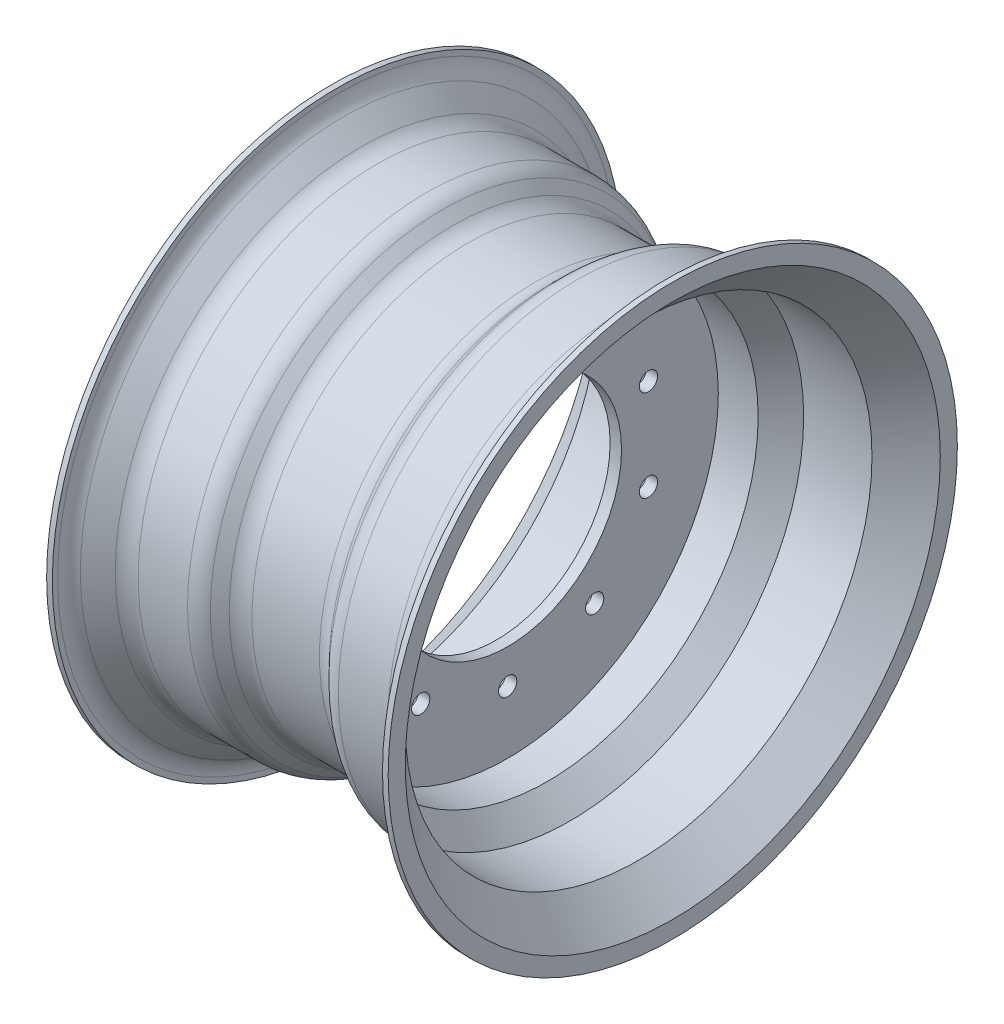
SolidWorks part; units mm, degrees
ref_plane "Front Plane" through (0, 0, 0) normal (0, 0, 1) x (1, 0, 0)
ref_plane "Top Plane" through (0, 0, 0) normal (0, 1, 0) x (1, 0, 0)
ref_plane "Right Plane" through (0, 0, 0) normal (1, 0, 0) x (0, 0, -1)
sketch "Sketch1" plane through (0, 0, 0) normal (0, 0, 1) x (1, 0, 0)
  line L0 (0, 221.1779) -> (0, 185) construction
  line L1 (0, 0) -> (-419.7995, 0) construction
  line L2 (-150, 250) -> (-150, 235)
  line L3 (-150, 235) -> (-120, 205)
  line L4 (-120, 205) -> (-60, 205)
  line L5 (-60, 205) -> (-40, 185)
  line L6 (-40, 185) -> (-5, 185)
  line L7 (60, 205) -> (40, 185)
  line L8 (120, 205) -> (60, 205)
  line L9 (150, 235) -> (120, 205)
  line L10 (150, 250) -> (150, 235)
  line L11 (-145, 250) -> (-145, 237.0711)
  line L12 (-145, 237.0711) -> (-117.9289, 210)
  line L13 (-117.9289, 210) -> (-57.9289, 210)
  line L14 (-57.9289, 210) -> (-37.9289, 190)
  line L15 (-37.9289, 190) -> (37.9289, 190)
  line L16 (57.9289, 210) -> (37.9289, 190)
  line L17 (117.9289, 210) -> (57.9289, 210)
  line L18 (145, 237.0711) -> (117.9289, 210)
  line L19 (145, 250) -> (145, 237.0711)
  line L20 (-150, 250) -> (-145, 250)
  line L21 (145, 250) -> (150, 250)
  line L22 (5, 185) -> (40, 185)
  line L24 (-5, 185) -> (-5, 100)
  line L25 (-5, 100) -> (5, 100)
  line L26 (5, 185) -> (5, 100)
  line L27 (-40, 185) -> (40, 185) construction
  line L28 (0, 100) -> (0, 0) construction
  point P10 (0, 185)
  dimension "D1" = 250
  dimension "D2" = 15
  dimension "D3" = 30
  dimension "D4" = 60
  dimension "D5" = 20
  dimension "D6" = 40
  dimension "D7" = 135
  dimension "D8" = 135
  dimension "D9" = 135
  dimension "D10" = 135
  dimension "D12" = 5
  dimension "D13" = 10
  dimension "D14" = 100
  dimension "D11" = 5
revolve "Revolve1" add sketch "Sketch1" angle 360 about L1
fillet "Fillet1" radius 20 8 edges at (117.9289, 0, -210) (57.9289, 0, -210) (37.9289, 0, -190) (-37.9289, 0, -190) (-57.9289, 0, -210) (-117.9289, 0, -210) (145, 0, -237.0711) (-145, 0, -237.0711)
sketch "Sketch2" plane through (5, 0, 0) normal (1, 0, 0) x (0, 0, -1)
  circle A0 centre (0, 130) radius 8
  dimension "D1" = 16
  dimension "D2" = 130
extrude "Cut-Extrude1" cut sketch "Sketch2" against normal blind 10
pattern_circular "CirPattern1" count 10 over 360 about axis through (0, 0, 0) along (1, 0, 0) of "Cut-Extrude1"
